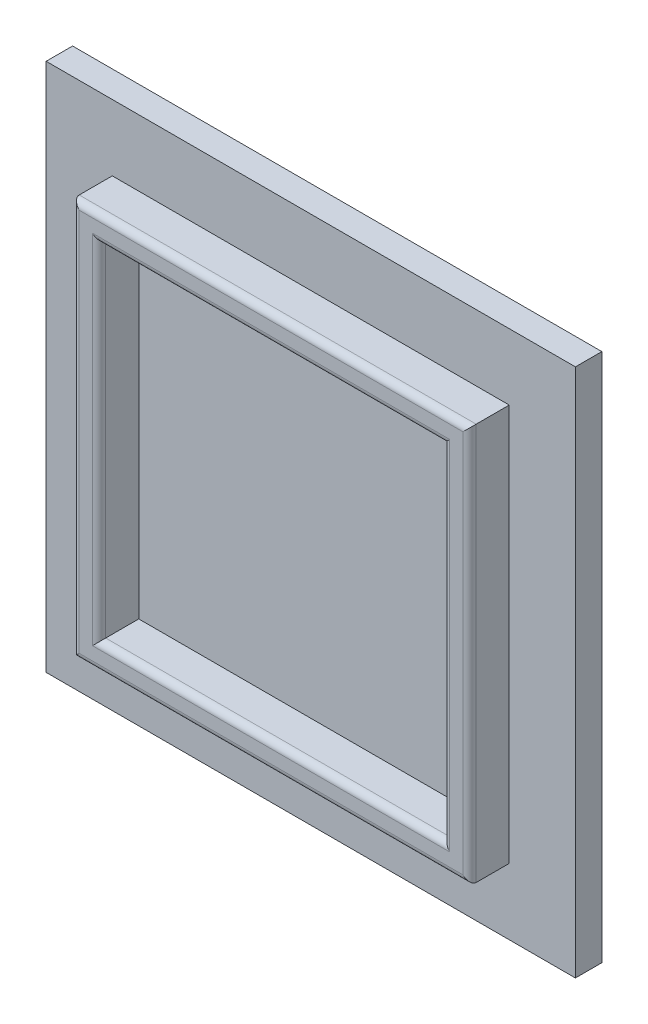
SolidWorks part; units mm, degrees
ref_plane "Front Plane" through (0, 0, 0) normal (0, 0, 1) x (1, 0, 0)
ref_plane "Top Plane" through (0, 0, 0) normal (0, 1, 0) x (1, 0, 0)
ref_plane "Right Plane" through (0, 0, 0) normal (1, 0, 0) x (0, 0, -1)
sketch "Sketch1" plane through (0, 0, 0) normal (0, 0, 1) x (1, 0, 0)
  line L1 (-25.1923, 15.1442) -> (14.8077, 15.1442)
  line L2 (-25.1923, 15.1442) -> (-25.1923, -24.8558)
  line L3 (-25.1923, -24.8558) -> (14.8077, -24.8558)
  line L4 (14.8077, 15.1442) -> (14.8077, -24.8558)
  dimension "D1" = 40
  dimension "D2" = 40
extrude "Boss-Extrude1" add sketch "Sketch1" along normal blind 2
sketch "Sketch2" plane through (0, 0, 2) normal (0, 0, 1) x (1, 0, 0)
  line L0 (-25.1923, 15.1442) -> (14.8077, -24.8558) construction
  line L1 (-25.1923, -24.8558) -> (14.8077, 15.1442) construction
  line L3 (9.8077, -19.8558) -> (-20.1923, -19.8558)
  line L4 (9.8077, -19.8558) -> (9.8077, 10.1442)
  line L5 (9.8077, 10.1442) -> (-20.1923, 10.1442)
  line L6 (-20.1923, -19.8558) -> (-20.1923, 10.1442)
  line L7 (9.8077, -19.8558) -> (-20.1923, 10.1442) construction
  line L8 (9.8077, 10.1442) -> (-20.1923, -19.8558) construction
  line L9 (7.8077, -17.8558) -> (-18.1923, -17.8558)
  line L10 (7.8077, -17.8558) -> (7.8077, 8.1442)
  line L11 (7.8077, 8.1442) -> (-18.1923, 8.1442)
  line L12 (-18.1923, -17.8558) -> (-18.1923, 8.1442)
  line L13 (7.8077, -17.8558) -> (-18.1923, 8.1442) construction
  line L14 (7.8077, 8.1442) -> (-18.1923, -17.8558) construction
  point P8 (-5.1923, -4.8558)
  point P9 (-5.1923, -4.8558)
  point P14 (-5.1923, -4.8558)
  dimension "D1" = 30
  dimension "D2" = 26
extrude "Boss-Extrude2" add sketch "Sketch2" along normal blind 3
fillet "Fillet1" radius 0.5 8 edges at (7.8077, -4.8558, 5) (-5.1923, 8.1442, 5) (-18.1923, -4.8558, 5) (-5.1923, -17.8558, 5) (-5.1923, -19.8558, 5) (-20.1923, -4.8558, 5) (9.8077, -4.8558, 5) (-5.1923, 10.1442, 5)
